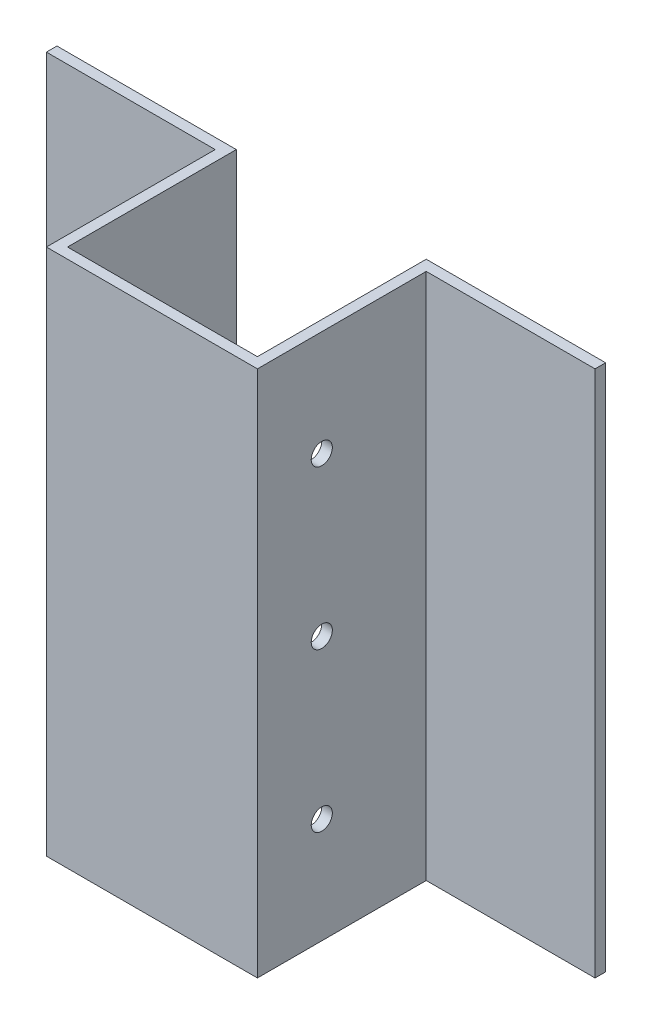
SolidWorks part; units mm, degrees
ref_plane "Plan de face" through (0, 0, 0) normal (0, 0, 1) x (1, 0, 0)
ref_plane "Plan de dessus" through (0, 0, 0) normal (0, 1, 0) x (1, 0, 0)
ref_plane "Plan de droite" through (0, 0, 0) normal (1, 0, 0) x (0, 0, -1)
sketch "Esquisse1" plane through (0, 0, 0) normal (0, 0, 1) x (1, 0, 0)
  line L1 (0, 0) -> (-45, 0)
  line L2 (0, 0) -> (0, 250)
  line L3 (0, 250) -> (-45, 250)
  line L4 (-45, 0) -> (-45, 250)
  dimension "D1" = 250
  dimension "D2" = 45
extrude "Boss.-Extru.1" add sketch "Esquisse1" along normal blind 5
sketch "Esquisse2" plane through (0, 0, 0) normal (1, 0, 0) x (0, 0, -1)
  line L1 (-5, 250) -> (75, 250)
  line L2 (-5, 250) -> (-5, 0)
  line L3 (-5, 0) -> (75, 0)
  line L4 (75, 250) -> (75, 0)
  dimension "D1" = 80
extrude "Boss.-Extru.2" add sketch "Esquisse2" along normal blind 5
sketch "Esquisse4" plane through (0, 0, -75) normal (0, 0, -1) x (-1, 0, 0)
  line L1 (0, 250) -> (-85, 250)
  line L2 (0, 250) -> (0, 0)
  line L3 (0, 0) -> (-85, 0)
  line L4 (-85, 250) -> (-85, 0)
  dimension "D1" = 250
  dimension "D2" = 85
extrude "Boss.-Extru.4" add sketch "Esquisse4" along normal blind 5
mirror "Symétrie1" about plane through (-45, 0, 5) normal (1, 0, 0) of "Boss.-Extru.1", "Boss.-Extru.2", "Boss.-Extru.4"
sketch "Esquisse5" plane through (5, 0, 0) normal (1, 0, 0) x (0, 0, -1)
  line L0 (-5, 0) -> (75, 0) construction
  line L1 (75, 250) -> (-5, 250) construction
  line L2 (-5, 250) -> (-5, 0) construction
  circle A0 centre (25.5, 125) radius 5
  circle A1 centre (25.5, 200) radius 5
  circle A2 centre (25.5, 50) radius 5
  dimension "D1" = 10
  dimension "D2" = 10
  dimension "D3" = 10
  dimension "D4" = 125
  dimension "D5" = 50
  dimension "D6" = 50
  dimension "D7" = 30.5
  dimension "D8" = 30.5
  dimension "D9" = 30.5
extrude "Enlèv. mat.-Extru.1" cut sketch "Esquisse5" against normal through all
